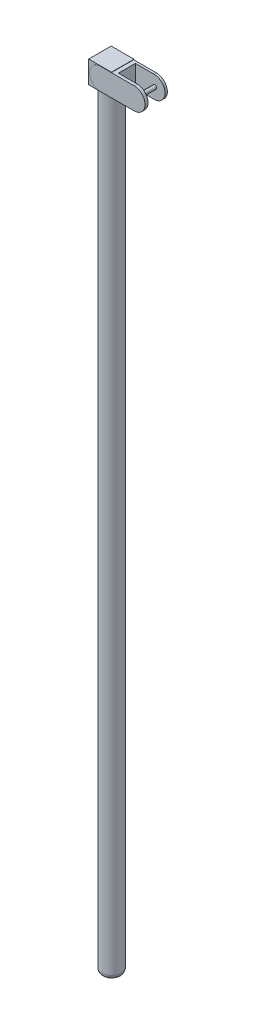
SolidWorks part; units mm, degrees
ref_plane "Ön Düzlem" through (0, 0, 0) normal (0, 0, 1) x (1, 0, 0)
ref_plane "Üst Düzlem" through (0, 0, 0) normal (0, 1, 0) x (1, 0, 0)
ref_plane "Sağ Düzlem" through (0, 0, 0) normal (1, 0, 0) x (0, 0, -1)
sketch "Çizim1" plane through (0, 0, 0) normal (0, 1, 0) x (1, 0, 0)
  circle A0 centre (0, 0) radius 2.1875
extrude "Yükseklik-Ekstrüzyon1" add sketch "Çizim1" along normal blind 177
fillet "Radyus1" radius 1 1 edges at (0, 0, 2.1875)
sketch "Çizim2" plane through (0, 177, 0) normal (0, 1, 0) x (1, 0, 0)
  line L0 (-2.666, 2.5737) -> (2.4492, 2.5737)
  line L1 (-2.666, 2.5737) -> (-2.666, -2.4693)
  line L2 (2.4492, 2.5737) -> (2.4492, -2.4693)
  line L3 (-2.666, -2.4693) -> (2.4492, -2.4693)
extrude "Yükseklik-Ekstrüzyon2" add sketch "Çizim2" against normal blind 5
sketch "Çizim3" plane through (0, 0, 0) normal (0, 0, 1) x (1, 0, 0)
  line L0 (0, 174.5006) -> (7.5476, 174.5006) construction
  line L1 (0, -2.7736) -> (0, 2.7736) construction
  line L2 (0, 176.9354) -> (7.5476, 176.9354)
  line L3 (0, 172.0658) -> (7.5476, 172.0658)
  arc A0 (0, 176.9354) -> (0, 172.0658) centre (0, 174.5006) ccw
  arc A1 (7.5476, 172.0658) -> (7.5476, 176.9354) centre (7.5476, 174.5006) ccw
  point P4 (3.7738, 174.5006)
  point P9 (7.5476, 174.5006)
extrude "Yükseklik-Ekstrüzyon3" add sketch "Çizim3" along normal mid plane 5
sketch "Çizim4" plane through (0, 176.9354, 0) normal (0, 1, 0) x (1, 0, 0)
  line L0 (3.3419, 1.9729) -> (3.3419, -1.816)
  line L1 (3.3419, 1.9729) -> (13.2978, 1.9729)
  line L2 (3.3419, -1.816) -> (13.2978, -1.816)
  line L3 (13.2978, 1.9729) -> (13.2978, -1.816)
extrude "Kes-Ekstrüzyon1" cut sketch "Çizim4" against normal blind 5
sketch "Çizim5" plane through (0, 0, 2.5) normal (0, 0, 1) x (1, 0, 0)
  circle A0 centre (7.7028, 174.5621) radius 0.4202
extrude "Yükseklik-Ekstrüzyon4" add sketch "Çizim5" against normal blind 5
